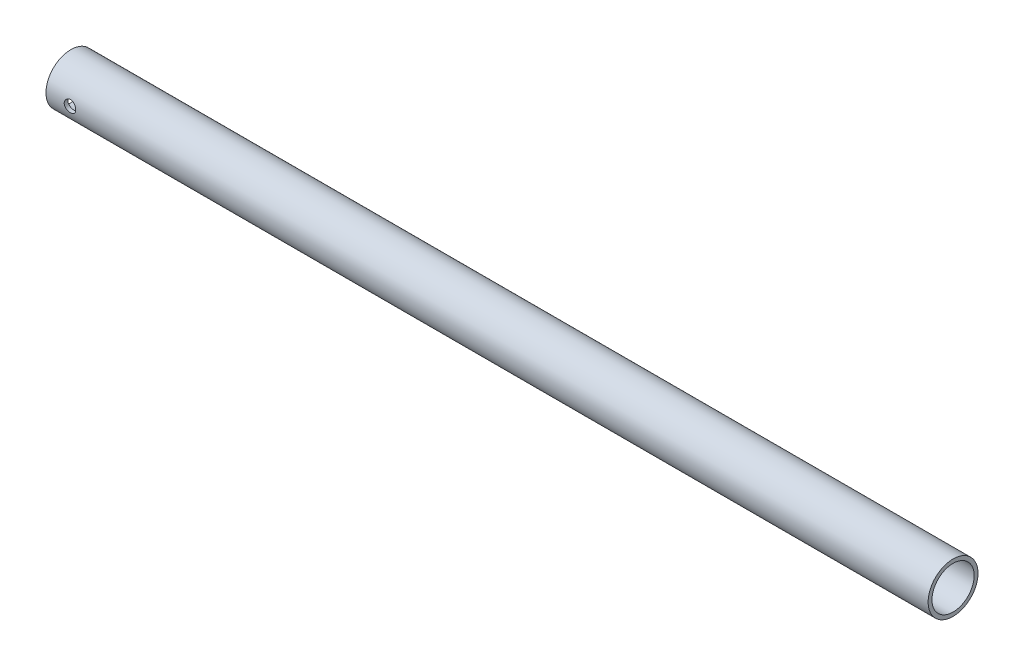
SolidWorks part; units mm, degrees
material "普通碳钢"
ref_plane "前视基准面" through (0, 0, 0) normal (0, 0, 1) x (1, 0, 0)
ref_plane "上视基准面" through (0, 0, 0) normal (0, 1, 0) x (1, 0, 0)
ref_plane "右视基准面" through (0, 0, 0) normal (1, 0, 0) x (0, 0, -1)
sketch "草图1" plane through (0, 0, 0) normal (1, 0, 0) x (0, 0, -1)
  circle A0 centre (0, 0) radius 13
  circle A1 centre (0, 0) radius 11
  dimension "D1" = 22
  dimension "D2" = 26
extrude "凸台-拉伸1" add sketch "草图1" along normal blind 460
sketch "草图4" plane through (0, 0, 0) normal (0, 1, 0) x (1, 0, 0)
  line L0 (0, 0) -> (460, 0) construction
  line L1 (460, -13) -> (460, 13) construction
  line L2 (0, 13) -> (0, -13) construction
  circle A0 centre (12.5, 0) radius 1.5
  circle A1 centre (441.5, 0) radius 1.5
  dimension "D2" = 3
  dimension "D3" = 3
  dimension "D1" = 12.5
  dimension "D4" = 18.5
extrude "切除-拉伸2" cut sketch "草图4" against normal through all
sketch "草图6" plane through (0, 0, 0) normal (0, 0, 1) x (1, 0, 0)
  line L0 (0, 0) -> (12.5, 0) construction
  circle A0 centre (12.5, 0) radius 3
  dimension "D2" = 6
  dimension "D1" = 12.5
extrude "切除-拉伸3" cut sketch "草图6" along normal through all
